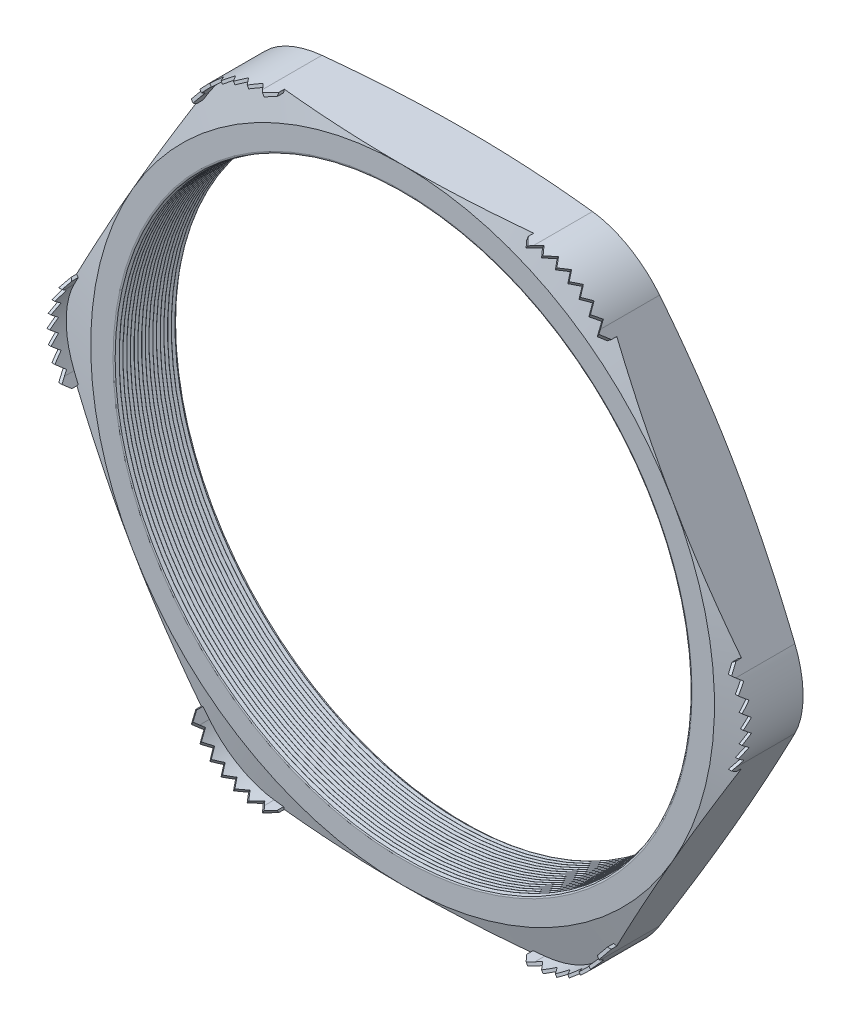
SolidWorks part; units mm, degrees
ref_plane "Front Plane" through (0, 0, 0) normal (0, 0, 1) x (1, 0, 0)
ref_plane "Top Plane" through (0, 0, 0) normal (0, 1, 0) x (1, 0, 0)
ref_plane "Right Plane" through (0, 0, 0) normal (1, 0, 0) x (0, 0, -1)
sketch "Sketch1" plane through (0, 0, 0) normal (0, 0, 1) x (1, 0, 0)
  line L1 (-29.476, 0) -> (-14.738, -25.527)
  line L2 (-14.738, -25.527) -> (14.738, -25.527)
  line L3 (14.738, -25.527) -> (29.476, 0)
  line L4 (29.476, 0) -> (14.738, 25.527)
  line L5 (14.738, 25.527) -> (-14.738, 25.527)
  line L6 (-14.738, 25.527) -> (-29.476, 0)
  circle A0 centre (0, 0) radius 25.527 construction
  circle A1 centre (0, 0) radius 23.495
  dimension "TS" = 46.99
  dimension "H" = 51.054
extrude "Extrude1" add sketch "Sketch1" along normal blind 5.08
fillet "Fillet1" radius 6.35 6 edges at (-14.738, 25.527, 2.54) (-29.476, 0, 2.54) (-14.738, -25.527, 2.54) (14.738, -25.527, 2.54) (29.476, 0, 2.54) (14.738, 25.527, 2.54)
sketch "Sketch2" plane through (0, 0, 5.08) normal (0, 0, 1) x (1, 0, 0)
  line L0 (-11.0718, 25.527) -> (-10.2082, 25.527)
  line L1 (11.0718, 25.527) -> (-11.0718, 25.527) construction
  line L2 (-16.5711, 22.352) -> (-17.0029, 21.6041)
  line L3 (-16.5711, 22.352) -> (-27.643, 3.175) construction
  line L4 (-11.0718, 25.2984) -> (-10.2082, 25.2984)
  line L5 (-16.3731, 22.2377) -> (-16.8049, 21.4898)
  line L6 (-17.0029, 21.6041) -> (-16.8049, 21.4898)
  line L7 (-10.2082, 25.527) -> (-10.2082, 25.2984)
  arc A0 (-11.0718, 25.2984) -> (-16.3731, 22.2377) centre (-11.0718, 19.177) ccw
  arc A1 (-11.0718, 25.527) -> (-16.5711, 22.352) centre (-11.0718, 19.177) ccw construction
  arc A4 (-11.0718, 25.527) -> (-16.5711, 22.352) centre (-11.0718, 19.177) ccw
  dimension "D1" = 0.8636
  dimension "D2" = 0.8636
  dimension "OFFSET" = 0.2286
fillet "Fillet3" radius 0.2032 2 edges at (23.495, 0, 0) (23.495, 0, 5.08)
sketch "Sketch3" plane through (0, 0, 0) normal (0, 1, 0) x (1, 0, 0)
  line L0 (-23.495, -5.08) -> (-23.495, -4.7867)
  line L2 (-23.495, -4.7867) -> (-23.749, -4.9334)
  line L3 (-23.749, -4.9334) -> (-23.495, -5.08)
  line L4 (-23.495, -0.2032) -> (-23.495, -4.8768) construction
  line L5 (-16.5711, -5.08) -> (-27.643, -5.08) construction
  dimension "D1" = 60
  dimension "D2" = 60
  dimension "D3" = 0.254
revolve "Cut-Revolve1" cut sketch "Sketch3" angle 360 about axis through (0, 0, 5.08) along (0, 0, -1)
pattern_linear "LPattern1" count 17 spacing 0.3048 along (0, 0, -1) of "Cut-Revolve1"
sketch "Sketch4" plane through (0, 0, 0) normal (0, 0, -1) x (-1, 0, 0)
  line L0 (-27.643, 3.175) -> (-16.5711, 22.352) construction
  circle A0 centre (0, 0) radius 25.527
extrude "Cut-Extrude1" cut sketch "Sketch4" against normal through all draft 75 flip side to cut
sketch "Sketch5" plane through (0, 0, 5.08) normal (0, 0, 1) x (1, 0, 0)
  line L0 (11.0718, 25.527) -> (-11.0718, 25.527) construction
  circle A0 centre (0, 0) radius 25.527
extrude "Cut-Extrude2" cut sketch "Sketch5" against normal through all draft 75 flip side to cut
extrude "Extrude2" add sketch "Sketch2" along normal blind 1.651 and the other way up to next
ref_plane "Plane1" through (-13.5066, 23.3941, 0) normal (0.5, -0.866, 0) x (0.866, 0.5, 0)
sketch "Sketch7" plane through (-13.5066, 23.3941, 0) normal (0.5, -0.866, 0) x (0.866, 0.5, 0)
  line L0 (-3.9229, 4.9974) -> (-3.3641, 5.6909)
  line L1 (-3.9229, 4.5534) -> (-3.9229, 6.731) construction
  line L2 (0, 1.3136) -> (0, 4.0135) construction
  line L4 (-3.3641, 5.6909) -> (-2.8053, 4.9974)
  line L5 (-1.1176, 5.6909) -> (-0.5588, 4.9974)
  line L6 (-2.2352, 5.6909) -> (-1.6764, 4.9974)
  line L7 (-0.5588, 4.9974) -> (0, 5.6909)
  line L8 (0, 5.6909) -> (0.5588, 4.9974)
  line L10 (1.1176, 5.6909) -> (1.6764, 4.9974)
  line L11 (2.2352, 5.6909) -> (2.794, 4.9974)
  line L12 (-2.8053, 4.9974) -> (-2.2352, 5.6909)
  line L13 (-1.6764, 4.9974) -> (-1.1176, 5.6909)
  line L14 (0.5588, 4.9974) -> (1.1176, 5.6909)
  line L15 (3.3641, 5.6909) -> (3.9229, 4.9974)
  line L16 (3.9229, 4.5534) -> (3.9229, 6.731) construction
  line L17 (-3.9229, 4.9974) -> (-3.9229, 6.731)
  line L19 (-3.9229, 6.731) -> (3.9229, 6.731)
  line L20 (3.9229, 6.731) -> (3.9229, 4.9974)
  line L23 (1.6764, 4.9974) -> (2.2352, 5.6909)
  line L25 (2.794, 4.9974) -> (3.3641, 5.6909)
  dimension "D1" = 1.7336
  dimension "D2" = 1.0401
  dimension "D3" = 0.5588
extrude "Cut-Extrude4" cut sketch "Sketch7" against normal through all
pattern_circular "CirPattern1" count 6 over 360 about axis through (0, 0, 0) along (0, 0, 1) of "Extrude2"
pattern_circular "CirPattern2" count 6 over 360 about axis through (0, 0, 0) along (0, 0, 1) of "Cut-Extrude4"
